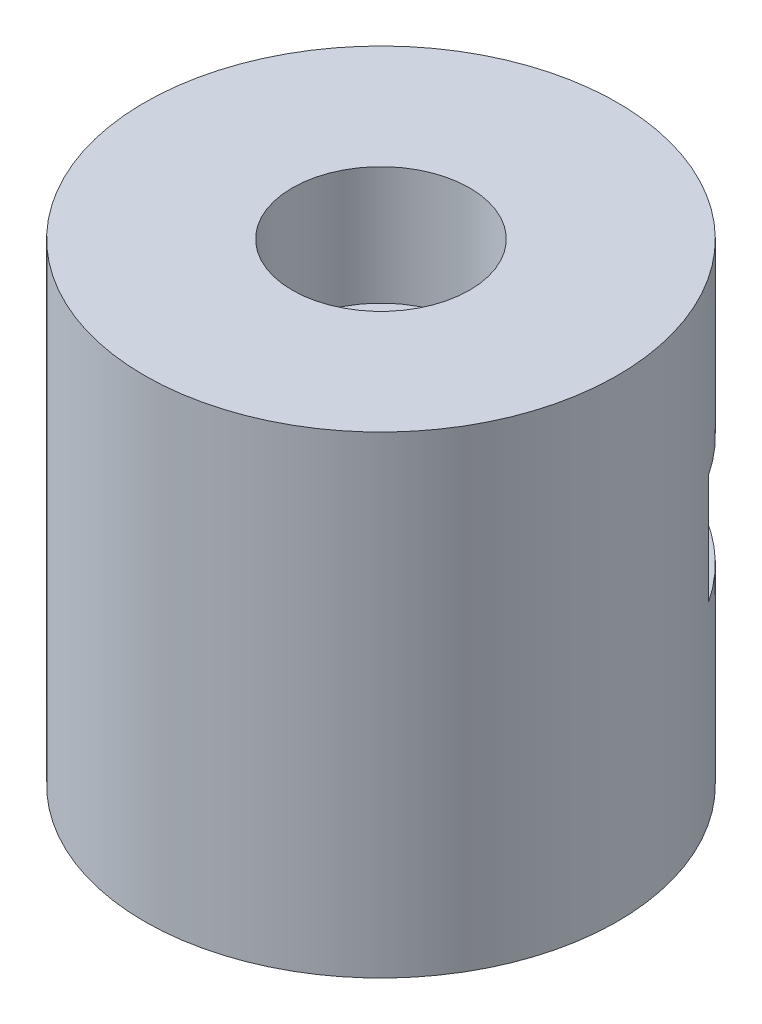
SolidWorks part; units mm, degrees
ref_plane "Front Plane" through (0, 0, 0) normal (0, 0, 1) x (1, 0, 0)
ref_plane "Top Plane" through (0, 0, 0) normal (0, 1, 0) x (1, 0, 0)
ref_plane "Right Plane" through (0, 0, 0) normal (1, 0, 0) x (0, 0, -1)
sketch "Sketch1" plane through (0, 0, 0) normal (0, 1, 0) x (1, 0, 0)
  circle A0 centre (0, 0) radius 20
  dimension "D1" = 40
extrude "Boss-Extrude1" add sketch "Sketch1" along normal blind 40
sketch "Sketch2" plane through (0, 40, 0) normal (0, 1, 0) x (1, 0, 0)
  circle A0 centre (0, 0) radius 7.5
  dimension "D1" = 15
extrude "Cut-Extrude1" cut sketch "Sketch2" against normal blind 10
ref_plane "Plane1" through (0, 0, -20) normal (0, 0, 1) x (1, 0, 0)
sketch "Sketch3" plane through (0, 0, -20) normal (0, 0, 1) x (1, 0, 0)
  line L1 (16.7023, 25.5407) -> (-16.7023, 25.5407)
  line L2 (16.7023, 25.5407) -> (16.7023, 16.2259)
  line L3 (16.7023, 16.2259) -> (-16.7023, 16.2259)
  line L4 (-16.7023, 25.5407) -> (-16.7023, 16.2259)
  line L5 (16.7023, 25.5407) -> (-16.7023, 16.2259) construction
  line L6 (16.7023, 16.2259) -> (-16.7023, 25.5407) construction
  point P0 (0, 20.8833)
extrude "Cut-Extrude2" cut sketch "Sketch3" along normal blind 10
